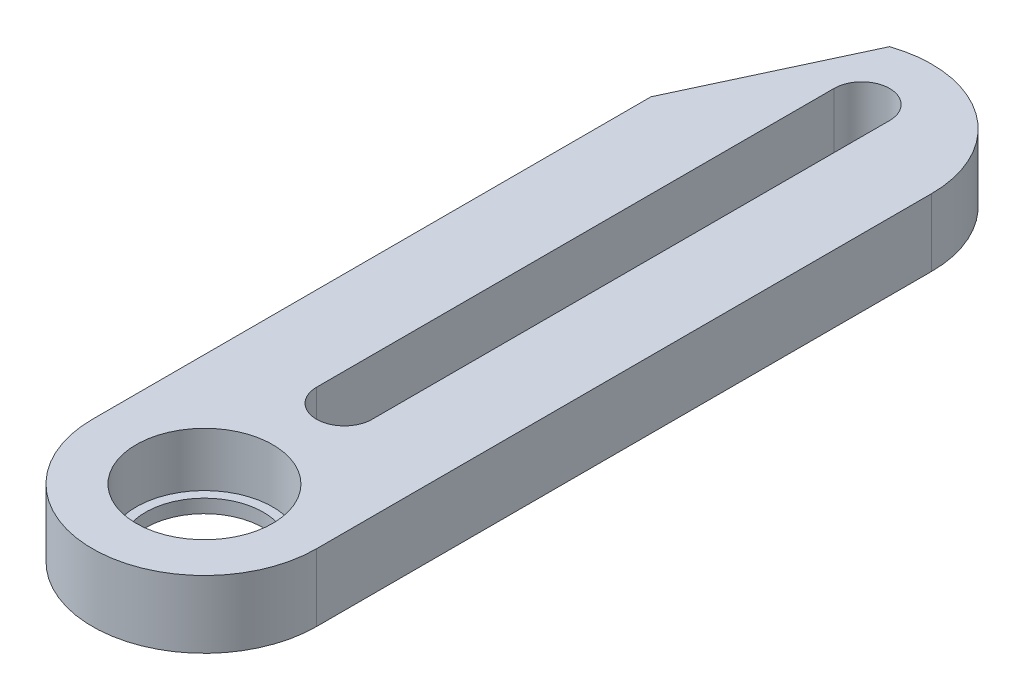
SolidWorks part; units mm, degrees
ref_plane "Front Plane" through (0, 0, 0) normal (0, 0, 1) x (1, 0, 0)
ref_plane "Top Plane" through (0, 0, 0) normal (0, 1, 0) x (1, 0, 0)
ref_plane "Right Plane" through (0, 0, 0) normal (1, 0, 0) x (0, 0, -1)
sketch "Sketch1" plane through (0, 0, 0) normal (0, 1, 0) x (1, 0, 0)
  line L0 (-6.65, 0) -> (-6.65, 36.5)
  line L1 (6.65, 36.5) -> (6.65, 0)
  line L2 (0, 39) -> (0, 8.3) construction
  line L3 (1.65, 39) -> (1.65, 8.3)
  line L4 (-1.65, 39) -> (-1.65, 8.3)
  line L5 (0, 40.65) -> (0, 43.15) construction
  line L7 (0, 6.65) -> (0, 4.05) construction
  circle A0 centre (0, 0) radius 4.05
  circle A1 centre (0, 0) radius 6.65
  arc A2 (-6.65, 36.5) -> (6.65, 36.5) centre (0, 36.5) cw
  arc A3 (1.65, 39) -> (-1.65, 39) centre (0, 39) ccw
  arc A4 (-1.65, 8.3) -> (1.65, 8.3) centre (0, 8.3) ccw
  point P8 (0, 23.65)
  point P16 (0, 6.65)
  dimension "D1" = 8.1
  dimension "D2" = 3.3
  dimension "D3" = 5
  dimension "D4" = 34
  dimension "D5" = 2.5
extrude "Boss-Extrude1" add sketch "Sketch1" along normal blind 4 contours A2 L0 A1 L1 A4 L4 A3 L3 | A1 A0
sketch "Sketch2" plane through (0, 0, 0) normal (0, 1, 0) x (1, 0, 0)
  circle A0 centre (0, 0) radius 4.05
  circle A1 centre (0, 0) radius 4.05 construction
extrude "Boss-Extrude2" add sketch "Sketch2" along normal blind 0.8
sketch "Sketch3" plane through (0, 0.8, 0) normal (0, 1, 0) x (1, 0, 0)
  circle A0 centre (0, 0) radius 3.5
  dimension "D1" = 7
extrude "Cut-Extrude1" cut sketch "Sketch3" against normal through all
sketch "Sketch4" plane through (0, 0, 0) normal (0, -1, 0) x (1, 0, 0)
  line L0 (-2.15, -42.7929) -> (-2.15, -12.7276) construction
  line L1 (-6.65, -33.1426) -> (-2.15, -42.7929)
  line L2 (-6.65, 0) -> (-6.65, -36.5) construction
  line L4 (-6.65, -33.1426) -> (-6.65, -36.5)
  line L5 (-1.65, -39) -> (-1.65, -8.3) construction
  arc A0 (-6.65, -36.5) -> (6.65, -36.5) centre (0, -36.5) ccw construction
  arc A1 (-6.65, -36.5) -> (-2.15, -42.7929) centre (0, -36.5) ccw
  dimension "D1" = 25
  dimension "D2" = 0.5
extrude "Cut-Extrude2" cut sketch "Sketch4" against normal through all
